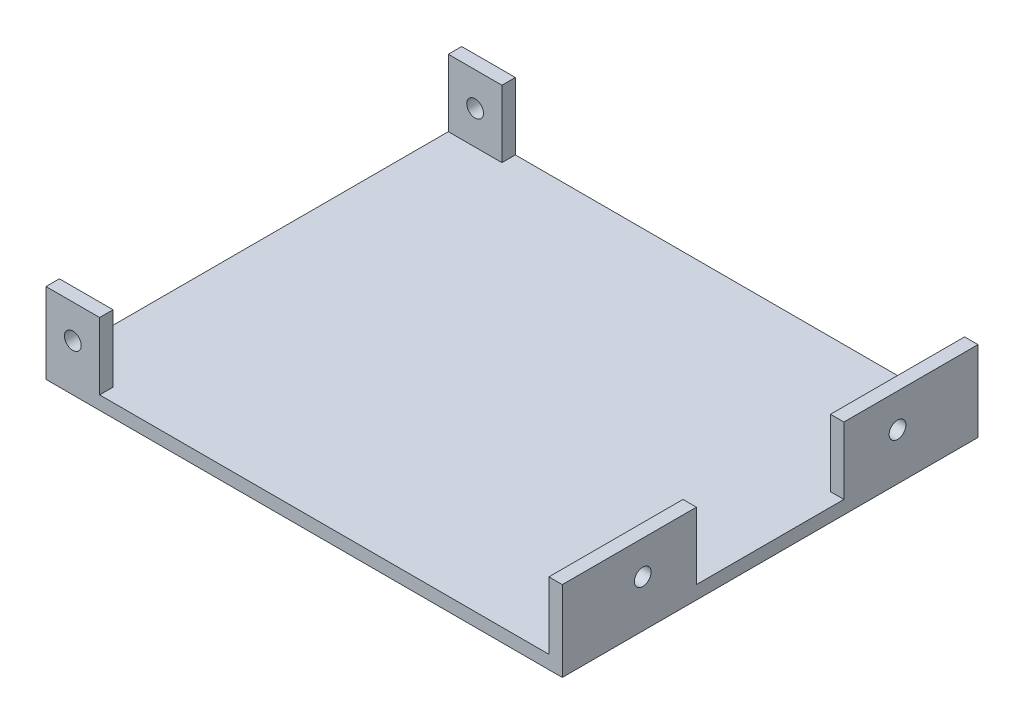
SolidWorks part; units mm, degrees
ref_plane "Front Plane" through (0, 0, 0) normal (0, 0, 1) x (1, 0, 0)
ref_plane "Top Plane" through (0, 0, 0) normal (0, 1, 0) x (1, 0, 0)
ref_plane "Right Plane" through (0, 0, 0) normal (1, 0, 0) x (0, 0, -1)
sketch "Sketch2" plane through (0, 0, 0) normal (0, 1, 0) x (1, 0, 0)
  line L1 (-42.6952, 46.8495) -> (34.3048, 46.8495)
  line L2 (-42.6952, 46.8495) -> (-42.6952, -15.1505)
  line L3 (-42.6952, -15.1505) -> (34.3048, -15.1505)
  line L4 (34.3048, 46.8495) -> (34.3048, -15.1505)
  dimension "D1" = 77
  dimension "D2" = 62
extrude "Boss-Extrude1" add sketch "Sketch2" along normal blind 2
sketch "Sketch3" plane through (0, 2, 0) normal (0, 1, 0) x (1, 0, 0)
  line L0 (-42.6952, -15.1505) -> (34.3048, -15.1505) construction
  line L1 (-42.6952, -13.1505) -> (-34.6952, -13.1505)
  line L2 (-42.6952, -13.1505) -> (-42.6952, -15.1505)
  line L3 (-42.6952, -15.1505) -> (-34.6952, -15.1505)
  line L4 (-34.6952, -13.1505) -> (-34.6952, -15.1505)
  line L5 (-42.6952, 46.8495) -> (-34.6952, 46.8495)
  line L6 (-42.6952, 46.8495) -> (-42.6952, 44.8495)
  line L7 (-42.6952, 44.8495) -> (-34.6952, 44.8495)
  line L8 (-34.6952, 46.8495) -> (-34.6952, 44.8495)
  line L9 (32.3048, 46.8495) -> (34.3048, 46.8495)
  line L10 (32.3048, 46.8495) -> (32.3048, 26.8495)
  line L11 (32.3048, 26.8495) -> (34.3048, 26.8495)
  line L12 (34.3048, 46.8495) -> (34.3048, 26.8495)
  line L13 (32.3048, 4.8495) -> (34.3048, 4.8495)
  line L14 (32.3048, 4.8495) -> (32.3048, -15.1505)
  line L15 (32.3048, -15.1505) -> (34.3048, -15.1505)
  line L16 (34.3048, 4.8495) -> (34.3048, -15.1505)
  line L17 (34.3048, 46.8495) -> (-42.6952, 46.8495) construction
  line L18 (-42.6952, 46.8495) -> (-42.6952, -15.1505) construction
  line L19 (34.3048, -15.1505) -> (34.3048, 46.8495) construction
  dimension "D1" = 8
  dimension "D2" = 8
  dimension "D3" = 2
  dimension "D4" = 2
  dimension "D5" = 0
  dimension "D6" = 0
  dimension "D7" = 0
  dimension "D8" = 0
  dimension "D9" = 0
  dimension "D10" = 2
  dimension "D11" = 2
  dimension "D12" = 0
  dimension "D13" = 0
  dimension "D14" = 0
  dimension "D15" = 20
  dimension "D16" = 20
extrude "Boss-Extrude2" add sketch "Sketch3" along normal blind 10 contours L6 L5 L8 L7 | L10 L9 L12 L11 | L14 L13 L16 L15 | L2 L1 L4 L3
sketch "Sketch4" plane through (0, 0, 15.1505) normal (0, 0, 1) x (1, 0, 0)
  line L1 (-42.6952, 12) -> (-42.6952, 0) construction
  line L3 (-34.6952, 2) -> (32.3048, 2) construction
  circle A0 centre (-38.6952, 7) radius 1.25
  dimension "D1" = 2.5
  dimension "D2" = 5
  dimension "D3" = 4
extrude "Cut-Extrude1" cut sketch "Sketch4" against normal through all
sketch "Sketch5" plane through (34.3048, 0, 0) normal (1, 0, 0) x (0, 0, -1)
  line L0 (-15.1505, 12) -> (-15.1505, 0) construction
  line L1 (46.8495, 12) -> (46.8495, 0) construction
  line L2 (4.8495, 12) -> (-15.1505, 12) construction
  line L3 (46.8495, 12) -> (26.8495, 12) construction
  circle A0 centre (-3.1505, 7) radius 1.25
  circle A1 centre (34.8495, 7) radius 1.25
  dimension "D1" = 2.5
  dimension "D2" = 2.5
  dimension "D3" = 12
  dimension "D4" = 12
  dimension "D5" = 5
  dimension "D6" = 5
extrude "Cut-Extrude2" cut sketch "Sketch5" against normal up to next
